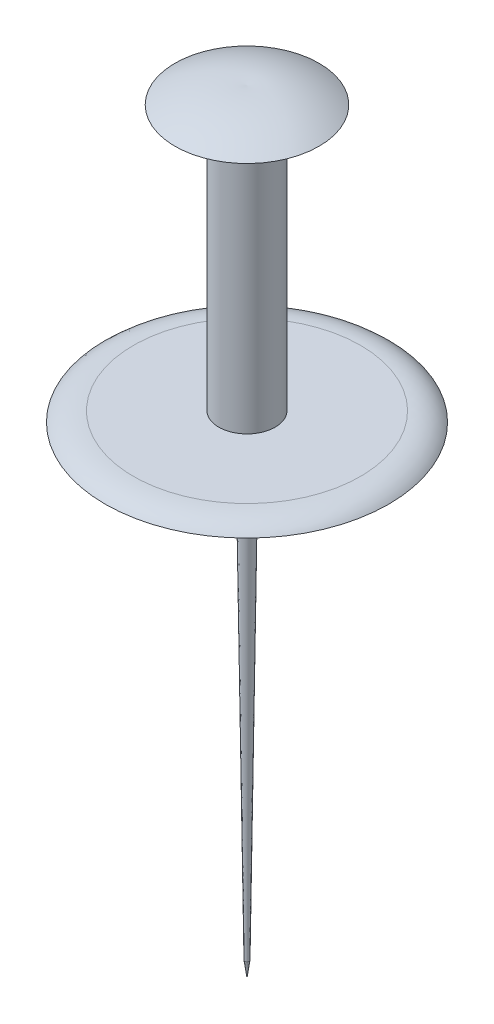
SolidWorks part; units mm, degrees
ref_plane "Front Plane" through (0, 0, 0) normal (0, 0, 1) x (1, 0, 0)
ref_plane "Top Plane" through (0, 0, 0) normal (0, 1, 0) x (1, 0, 0)
ref_plane "Right Plane" through (0, 0, 0) normal (1, 0, 0) x (0, 0, -1)
sketch "Sketch1" plane through (0, 0, 0) normal (0, 0, 1) x (1, 0, 0)
  line L0 (0, 0) -> (0, 70.2585)
  line L1 (0, 0) -> (0.194, 1.4072)
  line L2 (0.194, 1.4072) -> (0.7493, 43.7244)
  line L3 (0.7493, 43.7244) -> (12.8861, 43.7244)
  line L4 (10.3168, 44.624) -> (2.569, 44.624)
  line L5 (2.569, 44.624) -> (2.569, 68.7115)
  line L6 (2.569, 68.7115) -> (6.5425, 68.7115)
  spline S0 degree 2 poles (10.3168, 44.624) (12.0451, 44.6452) (12.8861, 43.7244) knots 0 0 0 1 1 1
  spline S1 degree 2 poles (0, 70.2585) (3.4249, 70.5287) (6.5425, 68.7115) knots 0 0 0 1 1 1
  point P8 (2.569, 68.7115)
revolve "Revolve1" add sketch "Sketch1" angle 360 about L0
